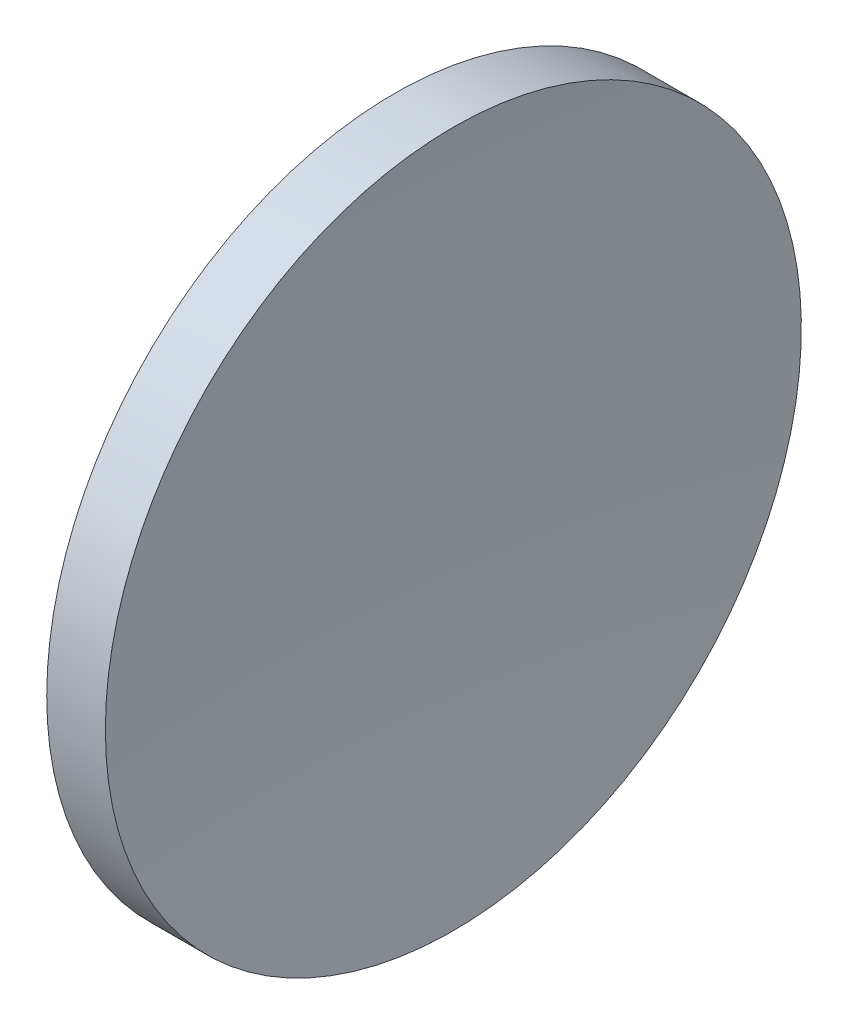
SolidWorks part; units mm, degrees
ref_plane "前视基准面" through (0, 0, 0) normal (0, 0, 1) x (1, 0, 0)
ref_plane "上视基准面" through (0, 0, 0) normal (0, 1, 0) x (1, 0, 0)
ref_plane "右视基准面" through (0, 0, 0) normal (1, 0, 0) x (0, 0, -1)
sketch "草图1" plane through (0, 0, 0) normal (0, 0, 1) x (1, 0, 0)
  line L0 (105.6218, 65.1556) -> (137.1869, 65.1556) construction
  line L1 (113.7394, 65.1556) -> (113.7394, 90.1556)
  line L2 (113.7394, 90.1556) -> (117.9527, 90.1556)
  line L3 (116.7394, 65.1556) -> (113.7394, 65.1556)
  arc A0 (117.9527, 90.1556) -> (116.7394, 65.1556) centre (374.9194, 65.1556) ccw
revolve "旋转1" add sketch "草图1" angle 360 about L0
